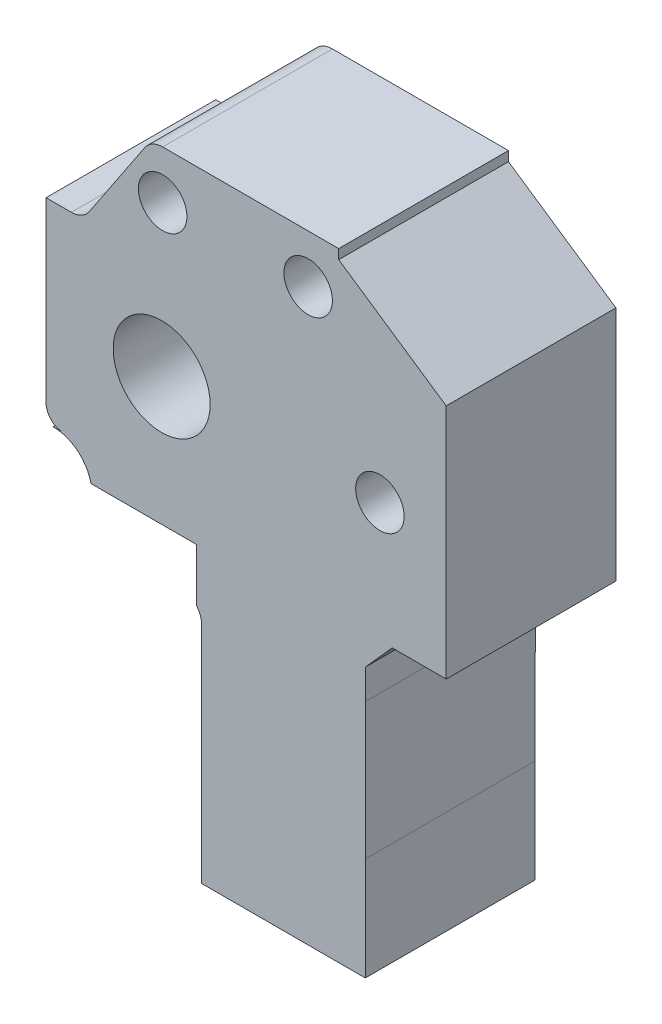
SolidWorks part; units mm, degrees
ref_plane "Front Plane" through (0, 0, 0) normal (0, 0, 1) x (1, 0, 0)
ref_plane "Top Plane" through (0, 0, 0) normal (0, 1, 0) x (1, 0, 0)
ref_plane "Right Plane" through (0, 0, 0) normal (1, 0, 0) x (0, 0, -1)
sketch "Sketch2" plane through (0, 0, 0) normal (0, 0, 1) x (1, 0, 0)
  line L0 (-6.1319, 29.8868) -> (5.8681, 29.8868)
  line L1 (8.3871, 29.0942) -> (17.2519, 23.0863)
  line L2 (17.2519, 20.1385) -> (17.2519, 4.7586)
  line L3 (12.7984, 3.5721) -> (10.6036, 1.1175)
  line L4 (10.6036, -1.3461) -> (10.5817, -12.6132)
  line L5 (10.5817, -12.6132) -> (10.5817, -21.1132)
  line L6 (10.5817, -21.1132) -> (-2.9161, -21.1132)
  line L7 (-2.9161, -21.1132) -> (-2.9161, -12.6132)
  line L8 (-2.9161, -12.6132) -> (-2.9161, -2.6132)
  line L9 (-3.3598, -1.4618) -> (-3.3598, 2.8868)
  line L10 (-3.3598, 2.8868) -> (-12.04, 2.8868)
  line L11 (-7.6129, 29.0942) -> (-12.1784, 22.2466)
  line L13 (-15.7481, 20.0891) -> (-15.7481, 6.8025)
  line L14 (-14.3324, 5.3868) -> (-15.1607, 5.3868)
  line L15 (17.2519, 23.0863) -> (17.2519, 20.1385)
  line L16 (10.6036, 1.1175) -> (10.6036, -1.3461)
  line L17 (-15.7481, 20.0891) -> (-15.7481, 21.454)
  line L19 (12.7984, 3.5721) -> (17.2519, 3.5721)
  line L20 (17.2519, 3.5721) -> (17.2519, 4.7586)
  line L22 (7.5945, 29.8868) -> (5.8681, 29.8868)
  line L23 (7.5945, 29.8868) -> (8.3871, 29.8868)
  line L24 (8.3871, 29.8868) -> (8.3871, 29.0942)
  line L25 (-13.6595, 21.454) -> (-15.7481, 21.454)
  arc A4 (-2.9161, -2.6132) -> (-3.3598, -1.4618) centre (-4.632, -2.6132) ccw
  arc A5 (-6.1319, 29.8868) -> (-7.6129, 29.0942) centre (-6.1319, 28.1068) ccw
  arc A6 (-12.1784, 22.2466) -> (-13.6595, 21.454) centre (-13.6595, 23.234) cw
  arc A8 (-15.7481, 6.8025) -> (-14.3324, 5.3868) centre (-14.3324, 6.8025) ccw
  arc A9 (-15.1607, 5.3868) -> (-12.04, 2.8868) centre (-15.1607, 2.1891) cw
  circle A10 centre (-6.2138, 13.4458) radius 4
  circle A11 centre (11.7862, 13.4458) radius 2
  circle A12 centre (-6.1319, 25.9063) radius 2
  circle A13 centre (5.8681, 25.9063) radius 2
  point P3 (-15.7481, 13.4458)
  dimension "D6" = 8
  dimension "D7" = 4
  dimension "D8" = 4
  dimension "D9" = 4
  dimension "D1" = 24
  dimension "D2" = 33
  dimension "D3" = 27
  dimension "D4" = 33
  dimension "D5" = 2.5
  dimension "D10" = 16
  dimension "D11" = 12
  dimension "D12" = 18
  dimension "D13" = 5.5
  dimension "D14" = 10
extrude "Boss-Extrude1" add sketch "Sketch2" along normal mid plane 14
